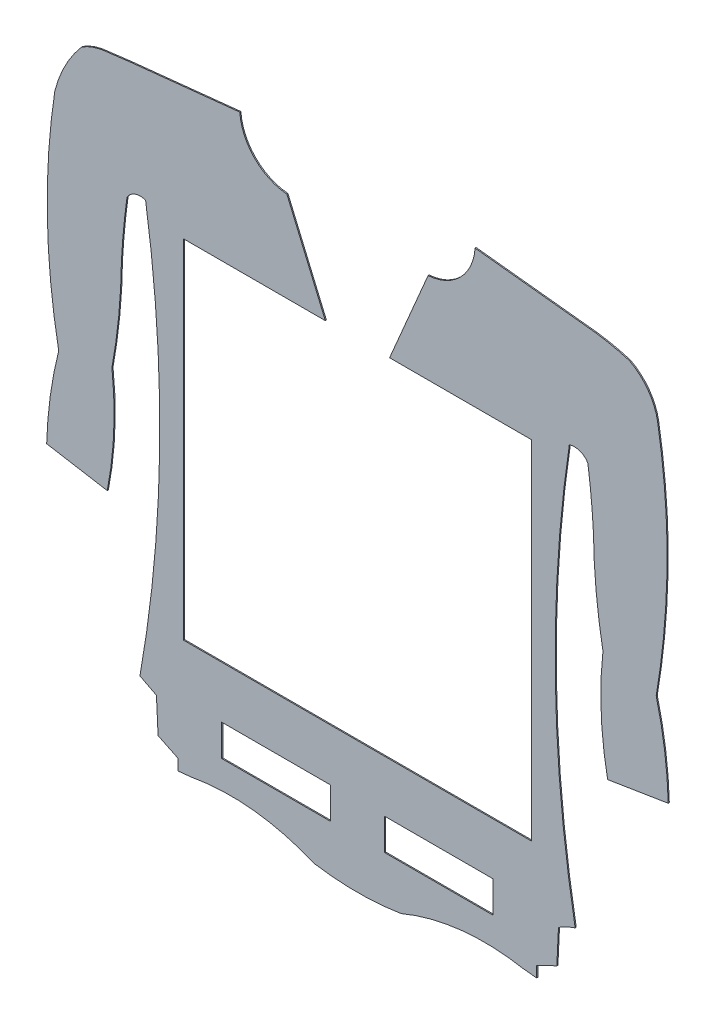
SolidWorks part; units mm, degrees
ref_plane "Alzado" through (0, 0, 0) normal (0, 0, 1) x (1, 0, 0)
ref_plane "Planta" through (0, 0, 0) normal (0, 1, 0) x (1, 0, 0)
ref_plane "Vista lateral" through (0, 0, 0) normal (1, 0, 0) x (0, 0, -1)
sketch "Model" plane through (0, 0, 0) normal (0, 0, 1) x (1, 0, 0)
  line L0 (35.7883, 21.7075) -> (34.5628, 21.5813)
  line L1 (34.5628, 21.5813) -> (34.5627, 22.5813)
  line L2 (34.5627, 22.5813) -> (32.7061, 23.4813)
  line L3 (32.7061, 23.4813) -> (32.5562, 26.6193)
  line L4 (32.5562, 26.6193) -> (31.0366, 27.4045)
  line L5 (28.0278, 40.6739) -> (22.4503, 41.6211)
  line L6 (27.3418, 75.5424) -> (27.5611, 75.5845)
  line L7 (27.5611, 75.5845) -> (30.1554, 75.9023)
  line L8 (30.1554, 75.9023) -> (40.2305, 76.953)
  line L9 (44.5587, 72.5837) -> (48.1018, 64.2618)
  line L10 (48.1018, 64.2618) -> (35.06, 64.2618)
  line L11 (35.06, 64.2618) -> (35.06, 32.2618)
  line L12 (35.06, 32.2618) -> (67.06, 32.2618)
  line L13 (67.06, 32.2618) -> (67.06, 64.2618)
  line L14 (67.06, 64.2618) -> (54.0181, 64.2618)
  line L15 (54.0181, 64.2618) -> (57.5612, 72.5837)
  line L16 (61.8886, 76.939) -> (73.033, 75.7315)
  line L17 (79.6711, 41.5675) -> (74.0924, 40.6692)
  line L18 (69.5645, 26.622) -> (69.4151, 23.484)
  line L19 (69.4151, 23.484) -> (67.5587, 22.5837)
  line L20 (67.5587, 22.5837) -> (67.5587, 21.5837)
  line L21 (67.5587, 21.5837) -> (66.3332, 21.7097)
  line L22 (63.56, 27.4837) -> (53.56, 27.4837)
  line L23 (53.56, 27.4837) -> (53.56, 24.5837)
  line L24 (53.56, 24.5837) -> (63.56, 24.5837)
  line L25 (63.56, 24.5837) -> (63.56, 27.4837)
  line L26 (38.56, 24.5837) -> (48.56, 24.5837)
  line L27 (48.56, 24.5837) -> (48.56, 27.4837)
  line L28 (48.56, 27.4837) -> (38.56, 27.4837)
  line L29 (38.56, 27.4837) -> (38.56, 24.5837)
  arc A0 (47.0571, 20.4744) -> (35.7883, 21.7075) centre (39.3646, 2.2827) ccw
  arc A1 (31.0366, 27.4045) -> (31.5587, 65.5837) centre (-84.9413, 48.0837) ccw
  arc A2 (31.5587, 65.5837) -> (29.8459, 64.9779) centre (31.0587, 64.273) ccw
  arc A3 (29.8459, 64.9779) -> (29.3326, 59.6604) centre (92.6323, 56.2336) ccw
  arc A4 (28.4592, 50.6951) -> (29.3326, 59.6604) centre (-23.4562, 60.2779) ccw
  arc A5 (28.0278, 40.6739) -> (28.4592, 50.6951) centre (-4.2677, 47.084) ccw
  arc A6 (23.5587, 49.5837) -> (22.4503, 41.6211) centre (59.0587, 40.5837) ccw
  arc A7 (23.2023, 70.1314) -> (23.5587, 49.5837) centre (83.4892, 60.9002) ccw
  arc A8 (25.6664, 74.862) -> (23.2023, 70.1314) centre (34.5351, 67.2354) ccw
  arc A9 (27.3418, 75.5424) -> (25.6664, 74.862) centre (28.3544, 70.646) ccw
  arc A10 (40.2305, 76.953) -> (44.5587, 72.5837) centre (44.9075, 77.2577) ccw
  arc A11 (57.5612, 72.5837) -> (61.8886, 76.939) centre (57.2124, 77.2577) ccw
  arc A12 (76.0952, 75.0701) -> (73.033, 75.7315) centre (70.3523, 55.8993) ccw
  arc A13 (78.6892, 71.5163) -> (76.0952, 75.0701) centre (73.7656, 70.646) ccw
  arc A14 (79.5632, 62.1462) -> (78.6892, 71.5163) centre (15.7195, 60.9172) ccw
  arc A15 (78.5612, 49.5837) -> (79.5632, 62.1462) centre (10.2354, 61.3546) ccw
  arc A16 (79.6711, 41.5675) -> (78.5612, 49.5837) centre (43.0612, 40.5837) ccw
  arc A17 (73.6598, 50.6943) -> (74.0924, 40.6692) centre (106.5921, 47.0933) ccw
  arc A18 (72.7874, 59.6604) -> (73.6598, 50.6943) centre (125.5801, 60.2718) ccw
  arc A19 (72.7874, 59.6604) -> (72.2741, 64.9779) centre (9.4877, 56.2336) ccw
  arc A20 (72.2741, 64.9779) -> (70.5612, 65.5837) centre (71.0612, 64.273) ccw
  arc A21 (70.5612, 65.5837) -> (71.1022, 27.3469) centre (187.2463, 48.1123) ccw
  arc A22 (71.1022, 27.3469) -> (69.5645, 26.622) centre (73.2329, 20.8335) ccw
  arc A23 (66.3332, 21.7097) -> (55.0646, 20.475) centre (62.7597, 2.2844) ccw
  arc A24 (47.0571, 20.4744) -> (55.0646, 20.475) centre (51.059, 45.6051) ccw
extrude "Saliente-Extruir1" add sketch "Model" along normal blind 0.1
